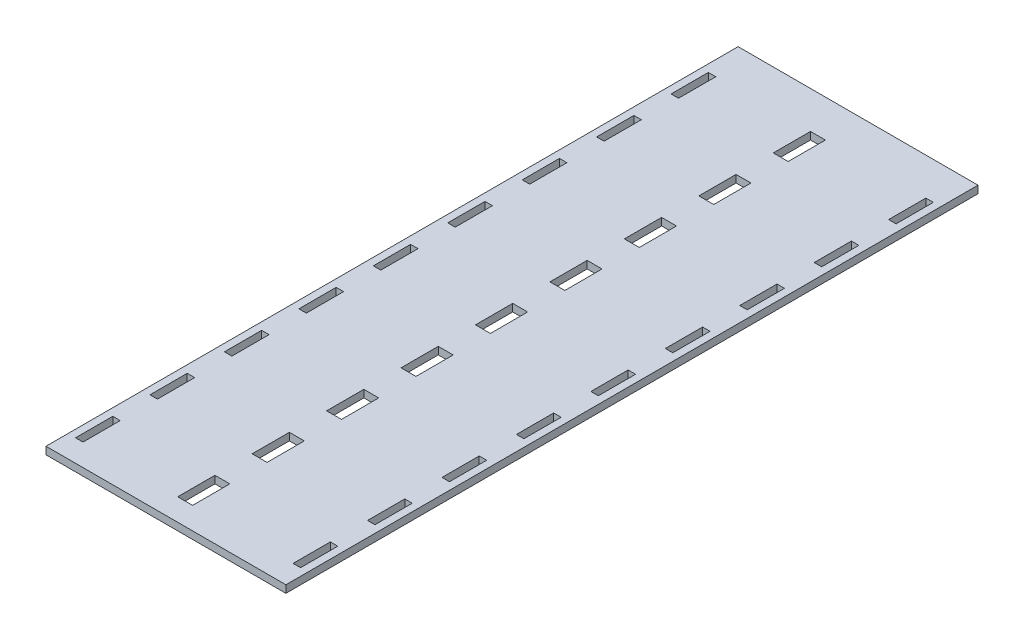
SolidWorks part; units mm, degrees
ref_plane "Спереди" through (0, 0, 0) normal (0, 0, 1) x (1, 0, 0)
ref_plane "Сверху" through (0, 0, 0) normal (0, 1, 0) x (1, 0, 0)
ref_plane "Справа" through (0, 0, 0) normal (1, 0, 0) x (0, 0, -1)
sketch "Эскиз1" plane through (0, 0, 0) normal (0, 1, 0) x (1, 0, 0)
  line L0 (4, -60) -> (-4, -60)
  line L1 (-62.9, 0) -> (66, 0)
  line L2 (0, 0) -> (0, -371.87) construction
  line L3 (66, 0) -> (66, -371.87)
  line L4 (-62.9, 0) -> (-62.9, -371.87)
  line L5 (4, -20) -> (-4, -20)
  line L6 (0, -20) -> (0, -40)
  line L7 (4, -40) -> (-4, -40)
  line L8 (-4, -20) -> (-4, -40)
  line L9 (0, -60) -> (0, -80)
  line L10 (4, -80) -> (-4, -80)
  line L11 (-4, -60) -> (-4, -80)
  line L12 (4, -100) -> (-4, -100)
  line L13 (0, -100) -> (0, -120)
  line L14 (4, -120) -> (-4, -120)
  line L15 (-4, -100) -> (-4, -120)
  line L16 (4, -140) -> (-4, -140)
  line L17 (0, -140) -> (0, -160)
  line L18 (4, -160) -> (-4, -160)
  line L19 (-4, -140) -> (-4, -160)
  line L20 (4, -180) -> (-4, -180)
  line L21 (0, -180) -> (0, -200)
  line L22 (4, -200) -> (-4, -200)
  line L23 (-4, -180) -> (-4, -200)
  line L24 (4, -220) -> (-4, -220)
  line L25 (0, -220) -> (0, -240)
  line L26 (4, -240) -> (-4, -240)
  line L27 (-4, -220) -> (-4, -240)
  line L28 (4, -260) -> (-4, -260)
  line L29 (0, -260) -> (0, -280)
  line L30 (4, -280) -> (-4, -280)
  line L31 (-4, -260) -> (-4, -280)
  line L32 (4, -300) -> (-4, -300)
  line L33 (0, -300) -> (0, -320)
  line L34 (4, -320) -> (-4, -320)
  line L35 (-4, -300) -> (-4, -320)
  line L36 (4, -340) -> (-4, -340)
  line L37 (0, -340) -> (0, -360)
  line L38 (4, -360) -> (-4, -360)
  line L39 (-4, -340) -> (-4, -360)
  line L40 (-54.9, -20) -> (-58.9, -20)
  line L41 (-54.9, -20) -> (-54.9, -40)
  line L42 (-54.9, -40) -> (-58.9, -40)
  line L43 (-58.9, -20) -> (-58.9, -40)
  line L44 (-54.9, -60) -> (-58.9, -60)
  line L45 (-54.9, -60) -> (-54.9, -80)
  line L46 (-54.9, -80) -> (-58.9, -80)
  line L47 (-58.9, -60) -> (-58.9, -80)
  line L48 (-54.9, -100) -> (-58.9, -100)
  line L49 (-54.9, -100) -> (-54.9, -120)
  line L50 (-54.9, -120) -> (-58.9, -120)
  line L51 (-58.9, -100) -> (-58.9, -120)
  line L52 (-54.9, -140) -> (-58.9, -140)
  line L53 (-54.9, -140) -> (-54.9, -160)
  line L54 (-54.9, -160) -> (-58.9, -160)
  line L55 (-58.9, -140) -> (-58.9, -160)
  line L56 (-54.9, -180) -> (-58.9, -180)
  line L57 (-54.9, -180) -> (-54.9, -200)
  line L58 (-54.9, -200) -> (-58.9, -200)
  line L59 (-58.9, -180) -> (-58.9, -200)
  line L60 (-54.9, -220) -> (-58.9, -220)
  line L61 (-54.9, -220) -> (-54.9, -240)
  line L62 (-54.9, -240) -> (-58.9, -240)
  line L63 (-58.9, -220) -> (-58.9, -240)
  line L64 (-54.9, -260) -> (-58.9, -260)
  line L65 (-54.9, -260) -> (-54.9, -280)
  line L66 (-54.9, -280) -> (-58.9, -280)
  line L67 (-58.9, -260) -> (-58.9, -280)
  line L68 (-54.9, -300) -> (-58.9, -300)
  line L69 (-54.9, -300) -> (-54.9, -320)
  line L70 (-54.9, -320) -> (-58.9, -320)
  line L71 (-58.9, -300) -> (-58.9, -320)
  line L72 (-54.9, -340) -> (-58.9, -340)
  line L73 (-54.9, -340) -> (-54.9, -360)
  line L74 (-54.9, -360) -> (-58.9, -360)
  line L75 (-58.9, -340) -> (-58.9, -360)
  line L76 (66, -371.87) -> (-62.9, -371.87)
  line L77 (58, -60) -> (62, -60)
  line L78 (58, -20) -> (62, -20)
  line L79 (58, -20) -> (58, -40)
  line L80 (58, -40) -> (62, -40)
  line L81 (62, -20) -> (62, -40)
  line L82 (58, -60) -> (58, -80)
  line L83 (58, -80) -> (62, -80)
  line L84 (62, -60) -> (62, -80)
  line L85 (58, -100) -> (62, -100)
  line L86 (58, -100) -> (58, -120)
  line L87 (58, -120) -> (62, -120)
  line L88 (62, -100) -> (62, -120)
  line L89 (58, -140) -> (62, -140)
  line L90 (58, -140) -> (58, -160)
  line L91 (58, -160) -> (62, -160)
  line L92 (62, -140) -> (62, -160)
  line L93 (58, -180) -> (62, -180)
  line L94 (58, -180) -> (58, -200)
  line L95 (58, -200) -> (62, -200)
  line L96 (62, -180) -> (62, -200)
  line L97 (58, -220) -> (62, -220)
  line L98 (58, -220) -> (58, -240)
  line L99 (58, -240) -> (62, -240)
  line L100 (62, -220) -> (62, -240)
  line L101 (58, -260) -> (62, -260)
  line L102 (58, -260) -> (58, -280)
  line L103 (58, -280) -> (62, -280)
  line L104 (62, -260) -> (62, -280)
  line L105 (58, -300) -> (62, -300)
  line L106 (58, -300) -> (58, -320)
  line L107 (58, -320) -> (62, -320)
  line L108 (62, -300) -> (62, -320)
  line L109 (58, -340) -> (62, -340)
  line L110 (58, -340) -> (58, -360)
  line L111 (58, -360) -> (62, -360)
  line L112 (4, -340) -> (4, -360)
  line L113 (4, -300) -> (4, -320)
  line L114 (4, -260) -> (4, -280)
  line L115 (4, -220) -> (4, -240)
  line L116 (4, -180) -> (4, -200)
  line L117 (4, -140) -> (4, -160)
  line L118 (4, -100) -> (4, -120)
  line L119 (4, -60) -> (4, -80)
  line L120 (4, -20) -> (4, -40)
  line L121 (62, -340) -> (62, -360)
  dimension "D1" = 371.87
  dimension "D2" = 20
  dimension "D3" = 20
  dimension "D4" = 8
  dimension "D6" = 50.9
  dimension "D7" = 4
  dimension "D9" = 4
  dimension "D10" = 54
  dimension "D11" = 4
  dimension "D5" = 9
  dimension "D8" = 9
  dimension "D12" = 9
extrude "Бобышка-Вытянуть1" add sketch "Эскиз1" along normal blind 4
